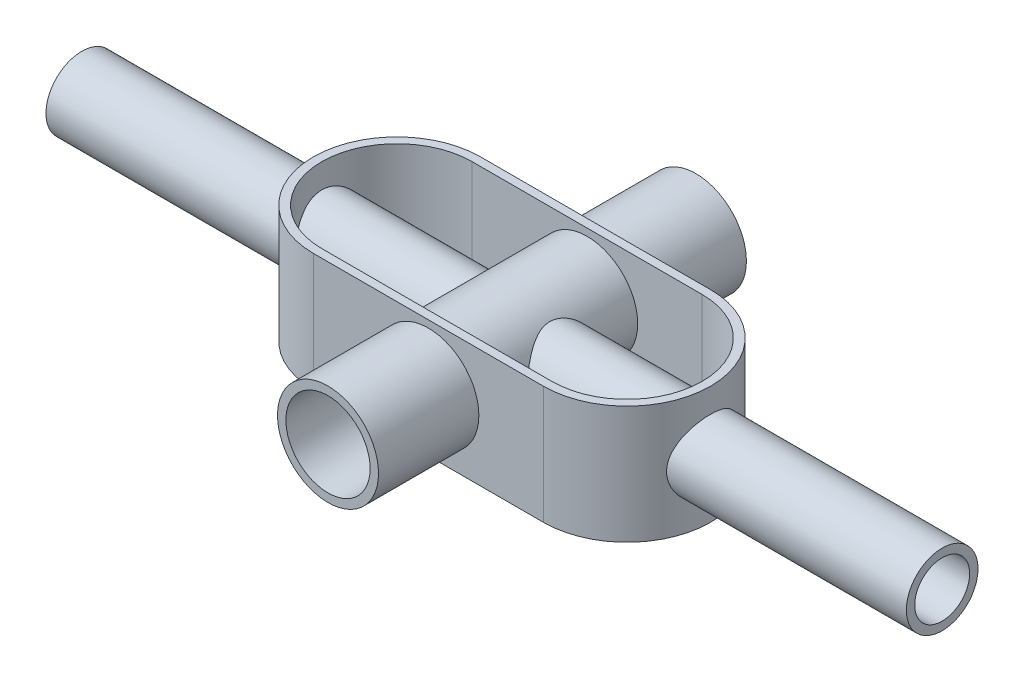
SolidWorks part; units mm, degrees
ref_plane "Front Plane" through (0, 0, 0) normal (0, 0, 1) x (1, 0, 0)
ref_plane "Top Plane" through (0, 0, 0) normal (0, 1, 0) x (1, 0, 0)
ref_plane "Right Plane" through (0, 0, 0) normal (1, 0, 0) x (0, 0, -1)
sketch "Sketch1" plane through (0, 0, 0) normal (0, 1, 0) x (1, 0, 0)
  line L0 (-34.9421, 0) -> (34.9421, 0) construction
  line L1 (-55, 0) -> (55, 0) construction
  line L2 (-34.9421, 25.3926) -> (34.9421, 25.3926)
  line L3 (-34.9421, -25.3926) -> (34.9421, -25.3926)
  line L4 (0, -55) -> (0, 55) construction
  arc A0 (-34.9421, 25.3926) -> (-34.9421, -25.3926) centre (-34.9421, 0) ccw
  arc A1 (34.9421, -25.3926) -> (34.9421, 25.3926) centre (34.9421, 0) ccw
  point P5 (0, 0)
extrude "Boss-Extrude1" add sketch "Sketch1" along normal blind 35.814
shell "Shell1" thickness 2.54
sketch "Sketch2" plane through (0, 0, 0) normal (1, 0, 0) x (0, 0, -1)
  line L0 (0, 19.6977) -> (0, -19.6977) construction
  circle A0 centre (0, 17.5252) radius 8.3443
extrude "Extrude-Thin1" add sketch "Sketch2" along normal mid plane 261.366 separate body thin
sketch "Sketch3" plane through (0, 0, 0) normal (0, 0, 1) x (1, 0, 0)
  line L0 (0, -19.8212) -> (0, 19.8212) construction
  circle A0 centre (0, 18.2999) radius 12.7989
extrude "Extrude-Thin2" add sketch "Sketch3" along normal mid plane 111.76 separate body thin
other "Uložit těla1"
